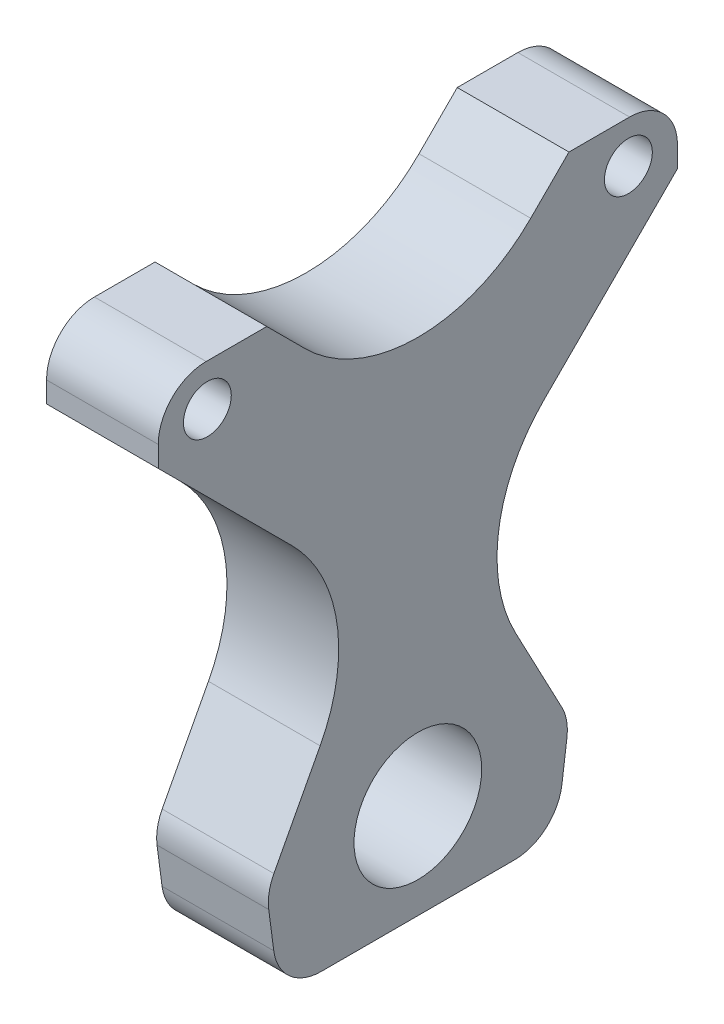
SolidWorks part; units mm, degrees
ref_plane "Front Plane" through (0, 0, 0) normal (0, 0, 1) x (1, 0, 0)
ref_plane "Top Plane" through (0, 0, 0) normal (0, 1, 0) x (1, 0, 0)
ref_plane "Right Plane" through (0, 0, 0) normal (1, 0, 0) x (0, 0, -1)
sketch "Sketch1" plane through (0, 0, 0) normal (1, 0, 0) x (0, 0, -1)
  line L0 (-16.2652, 11.0729) -> (-7.8895, 2.6972)
  line L1 (-13.2652, 15.3761) -> (-9.4671, 15.3761)
  line L2 (-16.2652, 12.3761) -> (-16.2652, 11.0729)
  line L4 (16.2652, 12.3761) -> (16.2652, 11.0729)
  line L5 (-9.3424, -16.3244) -> (-9.0273, -18.7198)
  line L6 (0, 5.909) -> (0, 26.3095) construction
  line L7 (-6.1208, -9.0493) -> (-9.0199, -14.5306)
  line L8 (0, 26.3095) -> (0, 5.909) construction
  line L9 (9.3424, -16.3244) -> (9.0273, -18.7198)
  line L10 (6.1208, -9.0493) -> (9.0199, -14.5306)
  line L11 (16.2652, 11.0729) -> (7.8895, 2.6972)
  line L12 (-9.4671, 15.3761) -> (-7.0711, 12.98)
  line L13 (7.0711, 12.98) -> (9.4671, 15.3761)
  line L14 (9.4671, 15.3761) -> (13.2652, 15.3761)
  line L15 (-6.053, -21.3286) -> (6.053, -21.3286)
  circle A0 centre (-13.1894, 12.756) radius 1.5
  circle A1 centre (13.1894, 12.756) radius 1.5
  circle A2 centre (0, -15.3761) radius 4
  arc A3 (-6.1208, -9.0493) -> (-7.8895, 2.6972) centre (-14.9605, -4.3739) ccw
  arc A4 (6.1208, -9.0493) -> (7.8895, 2.6972) centre (14.9605, -4.3739) cw
  arc A5 (-16.2652, 12.3761) -> (-13.2652, 15.3761) centre (-13.2652, 12.3761) cw
  arc A6 (16.2652, 12.3761) -> (13.2652, 15.3761) centre (13.2652, 12.3761) ccw
  arc A7 (-9.3424, -16.3244) -> (-9.0199, -14.5306) centre (-6.368, -15.9332) cw
  arc A8 (9.0199, -14.5306) -> (9.3424, -16.3244) centre (6.368, -15.9332) cw
  arc A9 (-9.0273, -18.7198) -> (-6.053, -21.3286) centre (-6.053, -18.3286) ccw
  arc A10 (9.0273, -18.7198) -> (6.053, -21.3286) centre (6.053, -18.3286) cw
  arc A11 (-7.0711, 12.98) -> (7.0711, 12.98) centre (0, 20.0511) ccw
  point P0 (0, 0)
  point P26 (2.6691, -2.5232)
  point P33 (-9.4671, -15.3761)
  point P36 (9.4671, -15.3761)
  point P39 (-8.6842, -21.3286)
  point P42 (8.6842, -21.3286)
  dimension "D1" = 8
  dimension "D3" = 10
  dimension "D4" = 10
  dimension "D5" = 3
  dimension "D6" = 3
  dimension "D7" = 3
  dimension "D8" = 3
  dimension "D9" = 10
  dimension "D2" = 19.2277
extrude "Boss-Extrude3" add sketch "Sketch1" along normal blind 7
